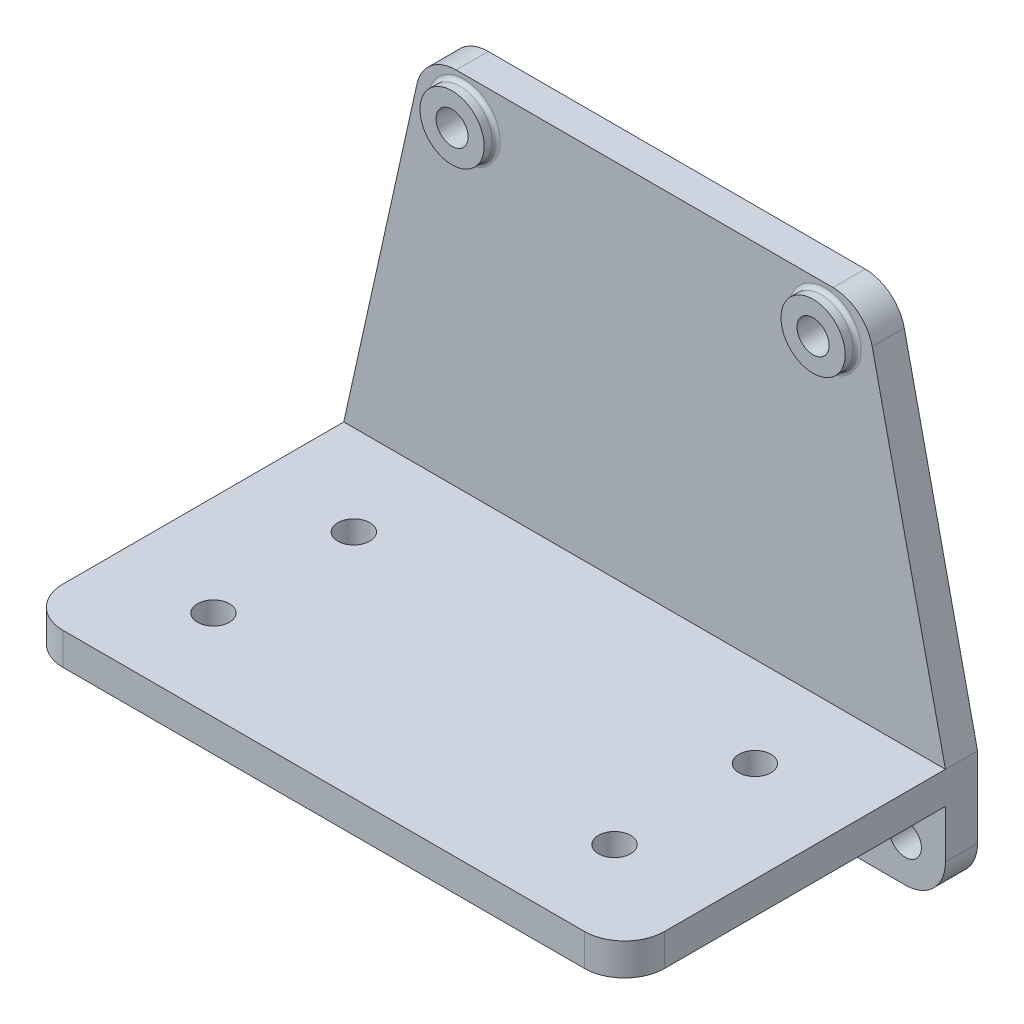
SolidWorks part; units mm, degrees
material "Сталь"
ref_plane "Спереди" through (0, 0, 0) normal (0, 0, 1) x (1, 0, 0)
ref_plane "Сверху" through (0, 0, 0) normal (0, 1, 0) x (1, 0, 0)
ref_plane "Справа" through (0, 0, 0) normal (1, 0, 0) x (0, 0, -1)
sketch "Эскиз1" plane through (0, 0, 0) normal (0, 0, 1) x (1, 0, 0)
  line L0 (0, 0) -> (75, 0)
  line L1 (75, 0) -> (75, 30)
  line L2 (75, 30) -> (55, 120)
  line L3 (55, 120) -> (0, 120)
  line L4 (0, 120) -> (0, 0)
  line L5 (0, 0) -> (0, 148.6143) construction
  dimension "D1" = 75
  dimension "D2" = 120
  dimension "D3" = 30
  dimension "D4" = 55
extrude "Бобышка-Вытянуть1" add sketch "Эскиз1" along normal blind 8
sketch "Эскиз2" plane through (0, 0, 8) normal (0, 0, 1) x (1, 0, 0)
  line L0 (0, 120) -> (0, 0) construction
  line L1 (0, 0) -> (75, 0) construction
  line L3 (55, 120) -> (0, 120) construction
  circle A0 centre (45, 110) radius 4
  circle A1 centre (0, 10) radius 4
  circle A2 centre (65, 10) radius 4
  dimension "D2" = 8
  dimension "D3" = 65
  dimension "D4" = 10
  dimension "D5" = 10
  dimension "D1" = 45
extrude "Вырез-Вытянуть1" cut sketch "Эскиз2" against normal through all
sketch "Эскиз3" plane through (0, 0, 8) normal (0, 0, 1) x (1, 0, 0)
  line L0 (0, 120) -> (0, 14) construction
  line L1 (75, 30) -> (0, 30)
  line L2 (75, 30) -> (75, 22)
  line L3 (75, 22) -> (0, 22)
  line L4 (0, 30) -> (0, 22)
  dimension "D1" = 8
extrude "Бобышка-Вытянуть2" add sketch "Эскиз3" along normal blind 80
sketch "Эскиз5" plane through (0, 30, 0) normal (0, 1, 0) x (1, 0, 0)
  line L0 (75, -48) -> (0, -48) construction
  line L1 (75, -88) -> (75, -8) construction
  line L2 (0, -88) -> (0, -8) construction
  line L4 (0, -88) -> (0, 0) construction
  circle A0 centre (50, -30.5) radius 4
  circle A1 centre (50, -65.5) radius 4
  dimension "D1" = 8
  dimension "D2" = 100
  dimension "D3" = 35
extrude "Вырез-Вытянуть2" cut sketch "Эскиз5" against normal through all
ref_plane "Плоскость1" through (35, 0, 0) normal (1, 0, 0) x (0, 0, -1)
sketch "Эскиз6" plane through (35, 0, 0) normal (1, 0, 0) x (0, 0, -1)
  line L0 (-88, 22) -> (-8, 0)
  line L1 (-8, 0) -> (-8, 22) construction
rib "Ребро1" sketch "Эскиз6" sketch "Эскиз6" thickness 8 extrusion direction parallel to sketch draft on no parameters "D1"=8
fillet "Скругление2" radius 10 3 edges at (55, 120, 4) (75, 0, 4) (75, 26, 88)
mirror "Зеркальное отражение1" about plane through (0, 120, 8) normal (1, 0, 0) of bodies 108
sketch "Эскиз7" plane through (0, 0, 8) normal (0, 0, 1) x (1, 0, 0)
  circle A0 centre (-45, 110) radius 8
  circle A1 centre (-45, 110) radius 4 construction
  circle A2 centre (45, 110) radius 4 construction
  circle A3 centre (-45, 110) radius 4
  circle A4 centre (45, 110) radius 4
  circle A5 centre (45, 110) radius 8
  dimension "D1" = 16
extrude "Бобышка-Вытянуть3" add sketch "Эскиз7" along normal blind 3
fillet "Скругление3" radius 1 2 edges at (53, 110, 8) (-37, 110, 8)
